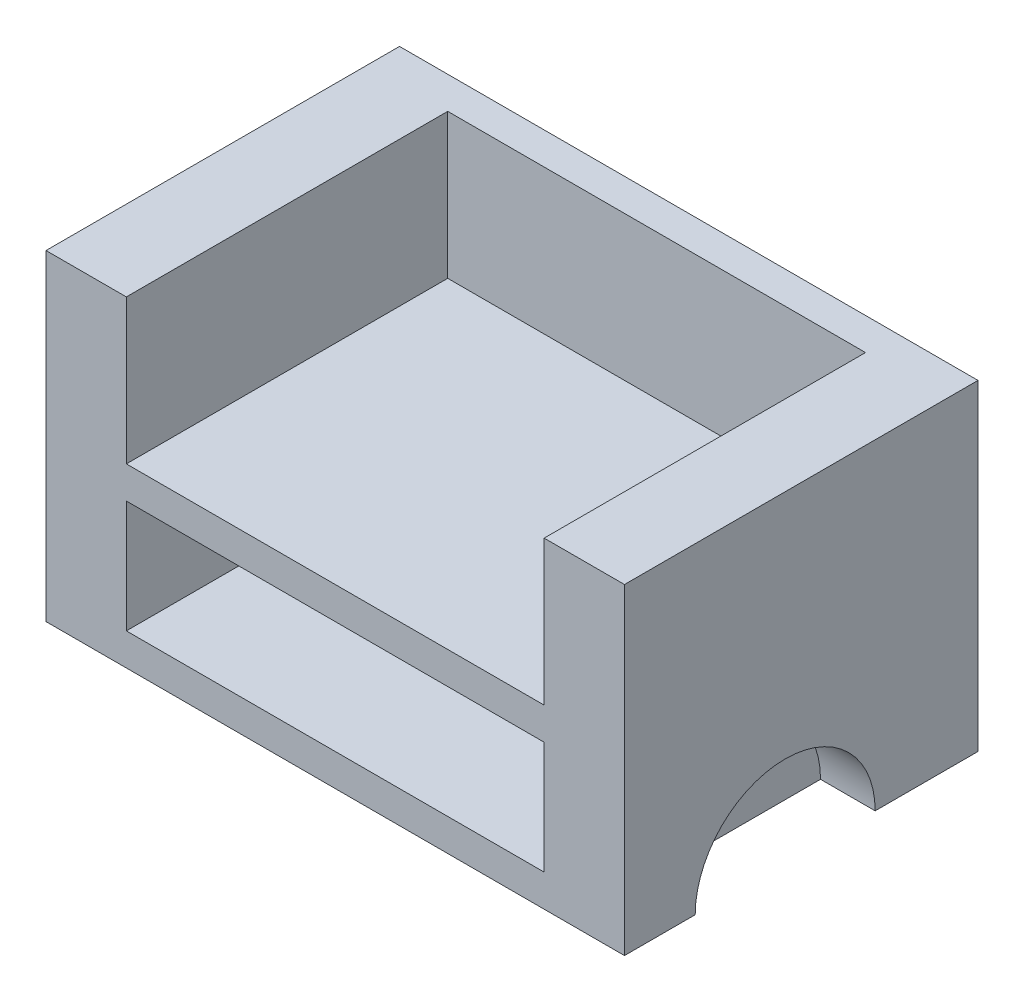
SolidWorks part; units mm, degrees
ref_plane "Front Plane" through (0, 0, 0) normal (0, 0, 1) x (1, 0, 0)
ref_plane "Top Plane" through (0, 0, 0) normal (0, 1, 0) x (1, 0, 0)
ref_plane "Right Plane" through (0, 0, 0) normal (1, 0, 0) x (0, 0, -1)
sketch "Sketch1" plane through (0, 0, 0) normal (0, 1, 0) x (1, 0, 0)
  line L1 (0, 120) -> (180, 120)
  line L2 (0, 120) -> (0, 0)
  line L3 (0, 0) -> (180, 0)
  line L4 (180, 120) -> (180, 0)
  dimension "D1" = 180
  dimension "D2" = 120
extrude "Boss-Extrude1" add sketch "Sketch1" along normal blind 100
sketch "Sketch2" plane through (0, 100, 0) normal (0, 1, 0) x (1, 0, 0)
  line L4 (180, 120) -> (0, 120) construction
  line L5 (25, 110) -> (155, 110)
  line L6 (25, 110) -> (25, 10)
  line L7 (25, 10) -> (155, 10)
  line L16 (155, 110) -> (155, 10)
  line L17 (0, 0) -> (180, 0) construction
  line L18 (0, 120) -> (0, 0) construction
  line L19 (180, 0) -> (180, 120) construction
  dimension "D1" = 10
  dimension "D2" = 10
  dimension "D3" = 25
  dimension "D4" = 25
extrude "Cut-Extrude1" cut sketch "Sketch2" against normal blind 90
sketch "Sketch3" plane through (180, 0, 0) normal (1, 0, 0) x (0, 0, -1)
  line L0 (0, 0) -> (120, 0) construction
  line L1 (32, 0) -> (88, 0)
  arc A0 (32, 0) -> (88, 0) centre (60, 0) cw
  dimension "28" = 28
sketch "Sketch4" plane through (0, 0, 0) normal (0, 1, 0) x (1, 0, 0)
  line L0 (90, 120) -> (90, 0) construction
  line L1 (180, 120) -> (0, 120) construction
  line L2 (0, 0) -> (180, 0) construction
extrude "Cut-Extrude2" cut sketch "Sketch3" against normal blind 17
sketch "Sketch5" plane through (0, 0, 0) normal (-1, 0, 0) x (0, 0, 1)
  line L0 (-120, 0) -> (0, 0) construction
  line L1 (-88, 0) -> (-32, 0)
  arc A0 (-88, 0) -> (-32, 0) centre (-60, 0) cw
  dimension "D1" = 28
extrude "Cut-Extrude3" cut sketch "Sketch5" against normal blind 17
sketch "Sketch6" plane through (0, 100, 0) normal (0, 1, 0) x (1, 0, 0)
  line L0 (180, 0) -> (180, 120) construction
  line L1 (0, 0) -> (180, 0)
  line L2 (0, 0) -> (0, 10)
  line L3 (0, 10) -> (180, 10)
  line L4 (180, 0) -> (180, 10)
  line L5 (25, 10) -> (155, 10) construction
extrude "Cut-Extrude4" cut sketch "Sketch6" against normal up to vertex
sketch "Sketch7" plane through (0, 0, -110) normal (0, 0, 1) x (1, 0, 0)
  line L0 (90, 0) -> (90, 40) construction
  line L1 (25, 10) -> (25, 100) construction
  line L2 (25, 55) -> (155, 55)
  line L3 (25, 55) -> (25, 45)
  line L4 (25, 45) -> (155, 45)
  line L5 (155, 55) -> (155, 45)
  line L6 (155, 10) -> (155, 100) construction
  line L7 (155, 100) -> (25, 100) construction
  line L10 (180, 0) -> (0, 0) construction
  dimension "D1" = 40
  dimension "D2" = 45
  dimension "D3" = 45
extrude "Boss-Extrude2" add sketch "Sketch7" along normal up to vertex (100 mm away)
